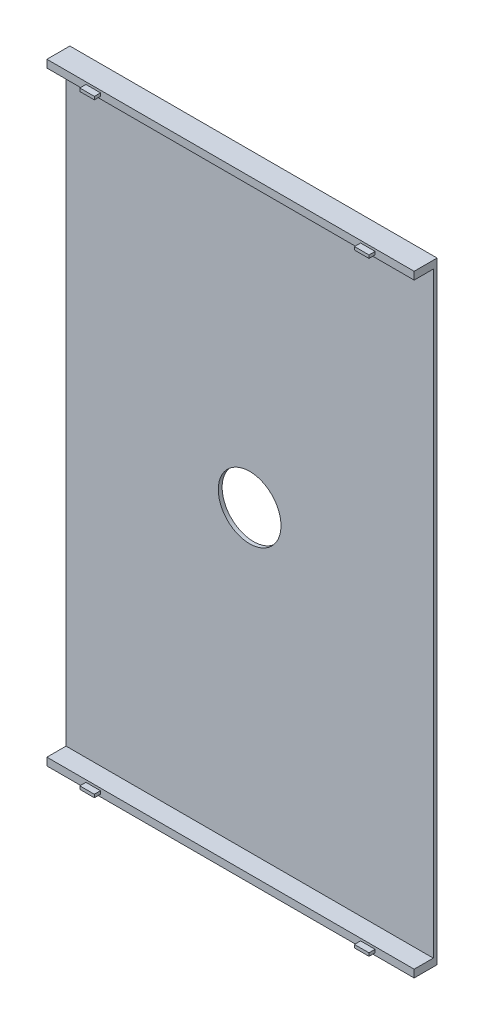
SolidWorks part; units mm, degrees
ref_plane "Front Plane" through (0, 0, 0) normal (0, 0, 1) x (1, 0, 0)
ref_plane "Top Plane" through (0, 0, 0) normal (0, 1, 0) x (1, 0, 0)
ref_plane "Right Plane" through (0, 0, 0) normal (1, 0, 0) x (0, 0, -1)
sketch "Sketch2" plane through (0, 0, 0) normal (0, 0, 1) x (1, 0, 0)
  line L0 (0, 0) -> (48, 0)
  line L1 (48, 0) -> (48, 80)
  line L2 (48, 80) -> (0, 80)
  line L3 (0, 80) -> (0, 0)
  dimension "D1" = 80
  dimension "D2" = 48
extrude "Boss-Extrude1" add sketch "Sketch2" along normal blind 0.5
sketch "Sketch3" plane through (0, 0, 0.5) normal (0, 0, 1) x (1, 0, 0)
  line L0 (0, 80) -> (48, 80)
  line L1 (48, 80) -> (48, 79)
  line L2 (48, 0) -> (48, 80) construction
  line L3 (48, 79) -> (0, 79)
  line L4 (0, 80) -> (0, 0) construction
  line L5 (0, 79) -> (0, 80)
  line L6 (0, 40) -> (48, 40) construction
  line L7 (48, 1) -> (0, 1)
  line L8 (48, 0) -> (48, 1)
  line L9 (0, 0) -> (48, 0)
  line L10 (0, 1) -> (0, 0)
  dimension "D1" = 1
extrude "Boss-Extrude2" add sketch "Sketch3" along normal blind 2.5
sketch "Sketch4" plane through (0, 0, 3) normal (0, 0, 1) x (1, 0, 0)
  line L0 (0, 80) -> (0, 79) construction
  line L1 (5.1, 79.7) -> (7, 79.7)
  line L2 (5.1, 79.7) -> (5.1, 79.3)
  line L3 (5.1, 79.3) -> (7, 79.3)
  line L4 (7, 79.7) -> (7, 79.3)
  line L5 (48, 80) -> (0, 80) construction
  line L6 (0, 79) -> (48, 79) construction
  line L7 (24, 80) -> (24, 79) construction
  line L8 (0, 79) -> (48, 79) construction
  line L9 (42.9, 79.3) -> (41, 79.3)
  line L10 (41, 79.7) -> (41, 79.3)
  line L11 (42.9, 79.7) -> (41, 79.7)
  line L12 (42.9, 79.7) -> (42.9, 79.3)
  point P6 (0, 79.5)
  point P7 (5.1, 79.5)
  dimension "D1" = 5.1
  dimension "D2" = 0.3
  dimension "D3" = 0.3
  dimension "D4" = 1.9
extrude "Boss-Extrude3" add sketch "Sketch4" along normal blind 0.8
sketch "Sketch5" plane through (0, 0, 3) normal (0, 0, 1) x (1, 0, 0)
  line L0 (0, 1) -> (0, 0) construction
  line L1 (5.1, 0.7) -> (7, 0.7)
  line L2 (5.1, 0.7) -> (5.1, 0.3)
  line L3 (5.1, 0.3) -> (7, 0.3)
  line L4 (7, 0.7) -> (7, 0.3)
  line L5 (48, 1) -> (0, 1) construction
  line L6 (0, 0) -> (48, 0) construction
  line L7 (24, 1) -> (24, 0) construction
  line L8 (42.9, 0.3) -> (41, 0.3)
  line L9 (41, 0.7) -> (41, 0.3)
  line L10 (42.9, 0.7) -> (41, 0.7)
  line L11 (42.9, 0.7) -> (42.9, 0.3)
  point P6 (5.1, 0.5)
  dimension "D1" = 5.1
  dimension "D2" = 0.3
  dimension "D3" = 0.3
  dimension "D4" = 1.9
extrude "Boss-Extrude4" add sketch "Sketch5" along normal blind 0.8
sketch "Sketch6" plane through (0, 0, 0) normal (0, 0, -1) x (-1, 0, 0)
  line L0 (-24, 80) -> (-24, 0) construction
  line L1 (-48, 80) -> (0, 80) construction
  line L2 (0, 0) -> (-48, 0) construction
  line L3 (0, 40) -> (-48, 40) construction
  line L4 (0, 80) -> (0, 0) construction
  line L5 (-48, 0) -> (-48, 80) construction
  circle A0 centre (-24, 40) radius 4.1
  dimension "D1" = 8.2
extrude "Cut-Extrude2" cut sketch "Sketch6" against normal blind 0.5
